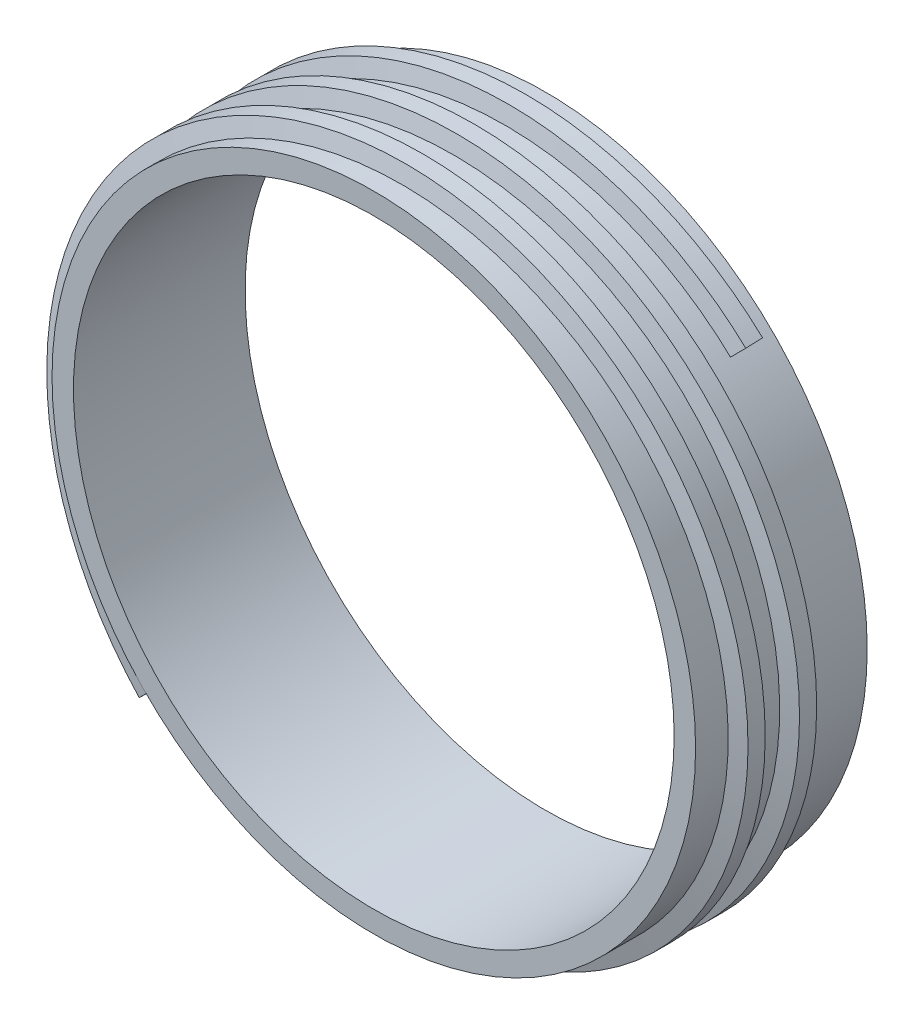
SolidWorks part; units mm, degrees
ref_plane "前视基准面" through (0, 0, 0) normal (0, 0, 1) x (1, 0, 0)
ref_plane "上视基准面" through (0, 0, 0) normal (0, 1, 0) x (1, 0, 0)
ref_plane "右视基准面" through (0, 0, 0) normal (1, 0, 0) x (0, 0, -1)
sketch "草图1" plane through (0, 0, 0) normal (0, 0, 1) x (1, 0, 0)
  circle A0 centre (0, 0) radius 37.5
  circle A1 centre (0, 0) radius 35
extrude "凸台-拉伸1" add sketch "草图1" along normal blind 20
ref_plane "基准面2" through (0, 0, 18.5) normal (0, 0, 1) x (1, 0, 0)
sketch "草图5" plane through (0, 0, 18.5) normal (0, 0, 1) x (1, 0, 0)
  circle A0 centre (0, 0) radius 37.35
curve "螺旋线/涡状线3" pitch 6 height 15 turns 2.5
ref_plane "基准面3" through (-26.4104, -26.4104, 18.5) normal (-0.7069, 0.7069, -0.0256) x (-0.0181, 0.0181, 0.9997)
sketch "草图6" plane through (-26.4104, -26.4104, 18.5) normal (-0.7069, 0.7069, -0.0256) x (-0.0181, 0.0181, 0.9997)
  line L0 (0, 3.5024) -> (0, -5.2084) construction
  line L1 (1.5, 0) -> (-1.5, 0)
  line L2 (1, -2) -> (-1, -2)
  line L3 (1.5, 0) -> (1, -2)
  line L4 (-1.5, 0) -> (-1, -2)
  dimension "D1" = 2
  dimension "D2" = 2
sweep "扫描1" add profiles "草图6" path "螺旋线/涡状线3"
